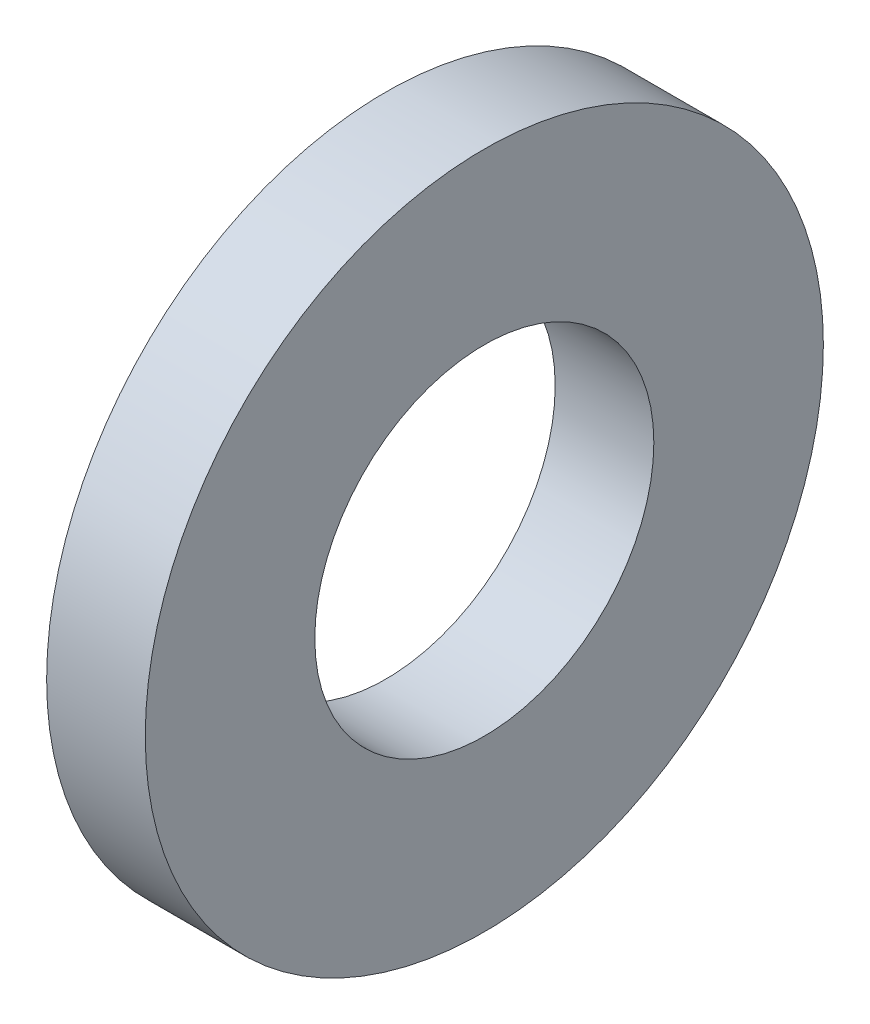
SolidWorks part; units mm, degrees
ref_plane "Plane1" through (0, 0, 0) normal (0, 0, 1) x (1, 0, 0)
ref_plane "Plane2" through (0, 0, 0) normal (0, 1, 0) x (1, 0, 0)
ref_plane "Plane3" through (0, 0, 0) normal (1, 0, 0) x (0, 0, -1)
sketch "Sketch1" plane through (0, 0, 0) normal (1, 0, 0) x (0, 0, -1)
  circle A0 centre (0, 0) radius 2.75
  circle A1 centre (0, 0) radius 5.5
  dimension "Insid_dia" = 5.5
  dimension "OutsideDia" = 11
extrude "Base-Extrude" add sketch "Sketch1" along normal blind 1.6
